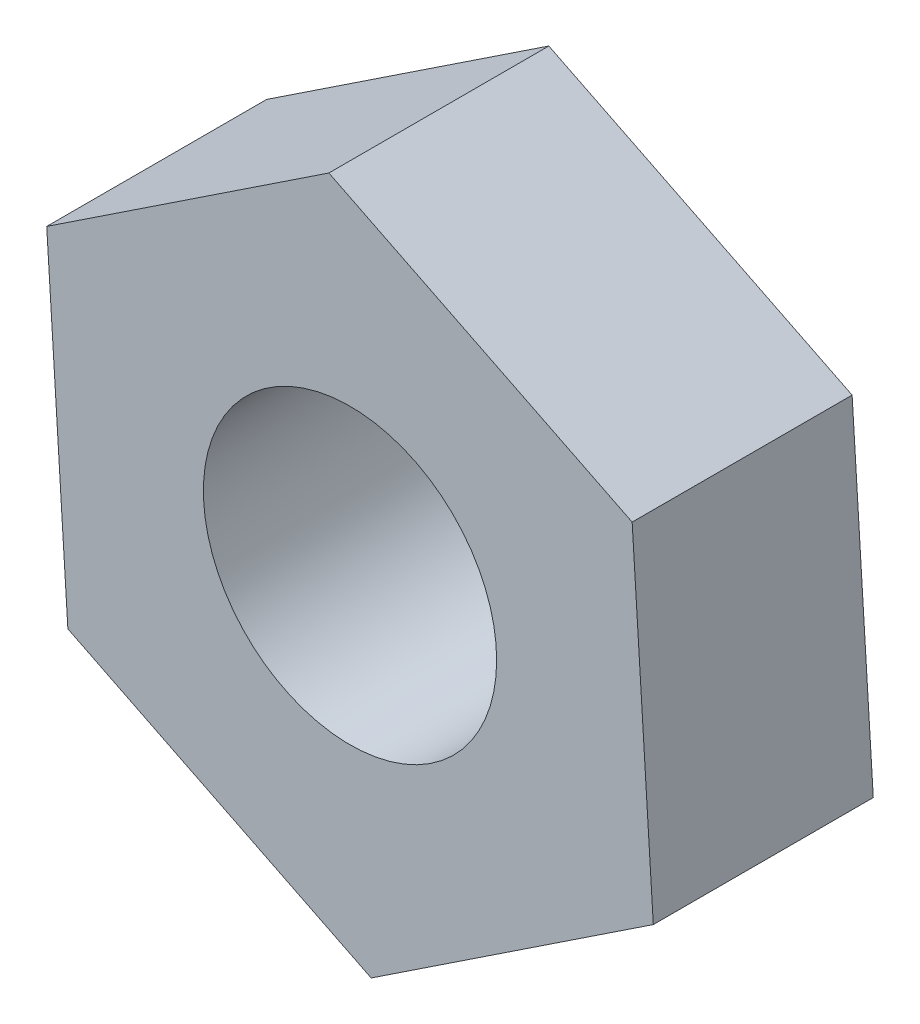
SolidWorks part; units mm, degrees
ref_plane "Front Plane" through (0, 0, 0) normal (0, 0, 1) x (1, 0, 0)
ref_plane "Top Plane" through (0, 0, 0) normal (0, 1, 0) x (1, 0, 0)
ref_plane "Right Plane" through (0, 0, 0) normal (1, 0, 0) x (0, 0, -1)
sketch "Sketch1" plane through (0, 0, 0) normal (0, 0, 1) x (1, 0, 0)
  line L1 (-1.924, -1.2774) -> (0.1443, -2.3049)
  line L2 (0.1443, -2.3049) -> (2.0682, -1.0275)
  line L3 (2.0682, -1.0275) -> (1.924, 1.2774)
  line L4 (1.924, 1.2774) -> (-0.1443, 2.3049)
  line L5 (-0.1443, 2.3049) -> (-2.0682, 1.0275)
  line L6 (-2.0682, 1.0275) -> (-1.924, -1.2774)
  circle A0 centre (0, 0) radius 2 construction
  dimension "D1" = 4
extrude "Boss-Extrude1" add sketch "Sketch1" along normal blind 1.5
sketch "Sketch2" plane through (0, 0, 1.5) normal (0, 0, 1) x (1, 0, 0)
  circle A0 centre (0, 0) radius 1
  dimension "D1" = 2
extrude "Cut-Extrude1" cut sketch "Sketch2" against normal through all
